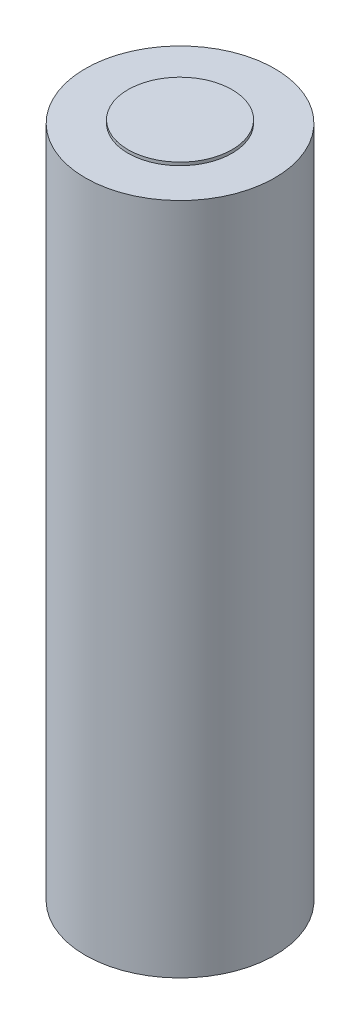
SolidWorks part; units mm, degrees
ref_plane "Front Plane" through (0, 0, 0) normal (0, 0, 1) x (1, 0, 0)
ref_plane "Top Plane" through (0, 0, 0) normal (0, 1, 0) x (1, 0, 0)
ref_plane "Right Plane" through (0, 0, 0) normal (1, 0, 0) x (0, 0, -1)
sketch "Sketch1" plane through (0, 0, 0) normal (0, 1, 0) x (1, 0, 0)
  circle A0 centre (0, 0) radius 9.1
  dimension "D1" = 18.2
extrude "Boss-Extrude1" add sketch "Sketch1" along normal blind 64.7
sketch "Sketch2" plane through (0, 64.7, 0) normal (0, 1, 0) x (1, 0, 0)
  circle A0 centre (0, 0) radius 5
  dimension "D1" = 10
extrude "Boss-Extrude2" add sketch "Sketch2" along normal blind 0.3
